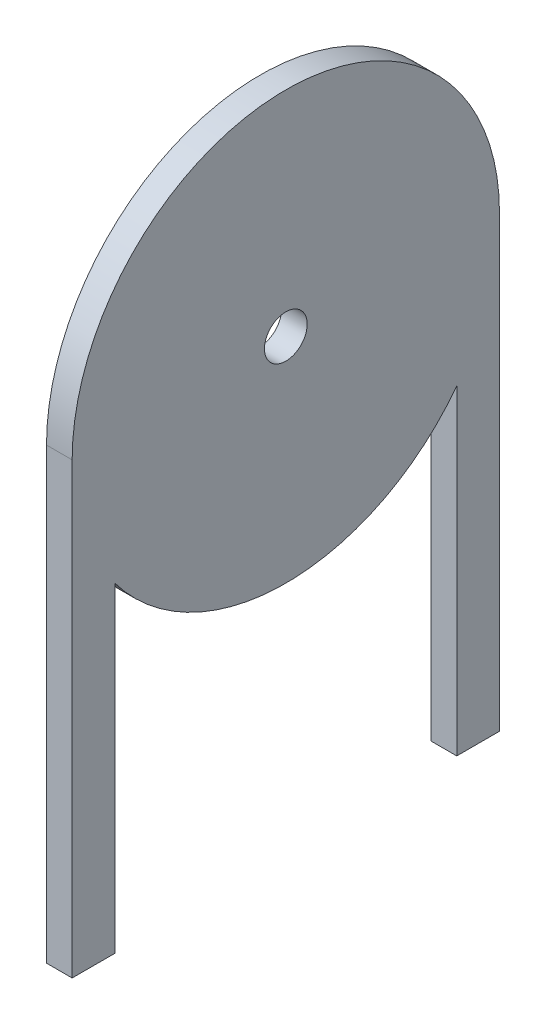
SolidWorks part; units mm, degrees
ref_plane "Front Plane" through (0, 0, 0) normal (0, 0, 1) x (1, 0, 0)
ref_plane "Top Plane" through (0, 0, 0) normal (0, 1, 0) x (1, 0, 0)
ref_plane "Right Plane" through (0, 0, 0) normal (1, 0, 0) x (0, 0, -1)
sketch "Sketch1" plane through (0, 0, 0) normal (1, 0, 0) x (0, 0, -1)
  line L0 (-25, 0) -> (-25, -52.5)
  line L1 (25, 0) -> (25, -52.5)
  line L2 (-20, -15) -> (-20, -52.5)
  line L3 (20, -15) -> (20, -52.5)
  line L4 (-25, -52.5) -> (-20, -52.5)
  line L5 (20, -52.5) -> (25, -52.5)
  arc A0 (-25, 0) -> (25, 0) centre (0, 0) cw
  circle A1 centre (0, 0) radius 2.5
  circle A2 centre (0, 0) radius 25
  dimension "D1" = 25
  dimension "D3" = 5
  dimension "D2" = 52.5
  dimension "D4" = 5
extrude "Boss-Extrude1" add sketch "Sketch1" along normal blind 3 contours A2 L0 L4 L2 | A0 A2 A1 | A2 L3 L5 L1
